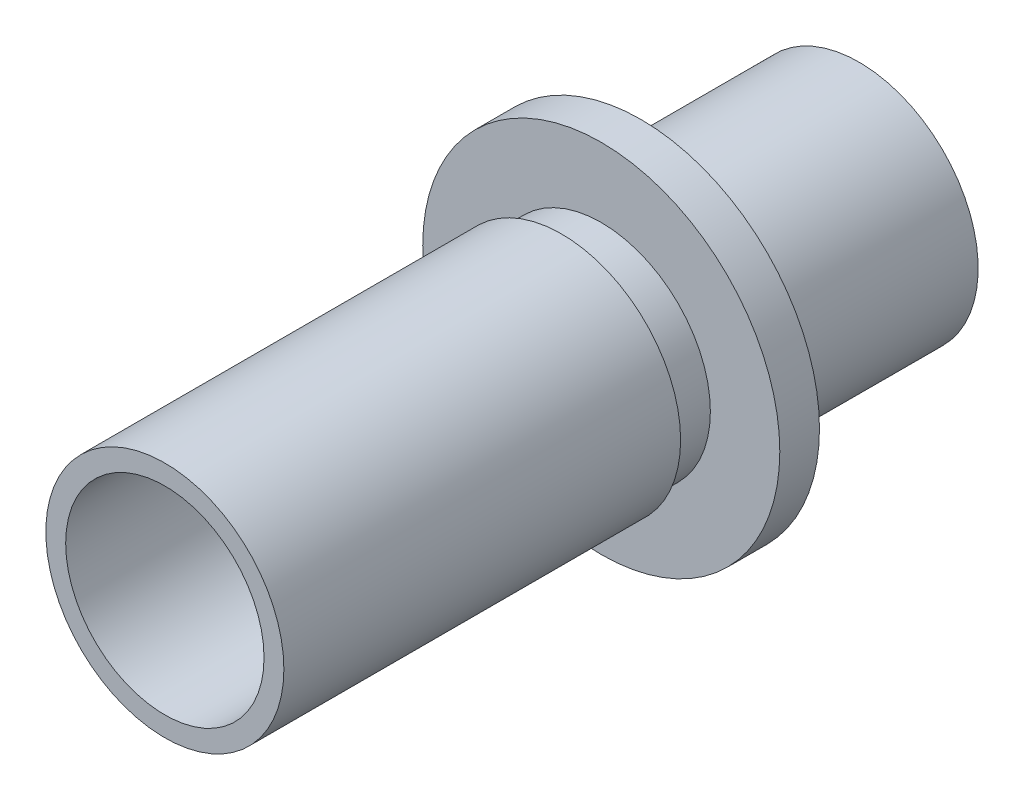
SolidWorks part; units mm, degrees
ref_plane "Plan de face" through (0, 0, 0) normal (0, 0, 1) x (1, 0, 0)
ref_plane "Plan de dessus" through (0, 0, 0) normal (0, 1, 0) x (1, 0, 0)
ref_plane "Plan de droite" through (0, 0, 0) normal (1, 0, 0) x (0, 0, -1)
sketch "Esquisse1" plane through (0, 0, 0) normal (0, 0, 1) x (1, 0, 0)
  circle A0 centre (0, 0) radius 5
  circle A1 centre (0, 0) radius 6
  dimension "D1" = 10
  dimension "D2" = 12
extrude "Boss.-Extru.1" add sketch "Esquisse1" along normal blind 10
sketch "Esquisse2" plane through (0, 0, 0) normal (0, 0, -1) x (-1, 0, 0)
  circle A0 centre (0, 0) radius 4.5
  circle A1 centre (0, 0) radius 6
  dimension "D1" = 12
  dimension "D2" = 9
extrude "Boss.-Extru.2" add sketch "Esquisse2" along normal blind 1
sketch "Esquisse3" plane through (0, 0, 10) normal (0, 0, 1) x (1, 0, 0)
  circle A0 centre (0, 0) radius 5
  circle A1 centre (0, 0) radius 9
  dimension "D1" = 10
  dimension "D2" = 18
extrude "Boss.-Extru.3" add sketch "Esquisse3" along normal blind 2
sketch "Esquisse4" plane through (0, 0, 12) normal (0, 0, 1) x (1, 0, 0)
  circle A0 centre (0, 0) radius 5
  circle A1 centre (0, 0) radius 5.5
  dimension "D1" = 10
  dimension "D2" = 11
extrude "Boss.-Extru.4" add sketch "Esquisse4" along normal blind 2
sketch "Esquisse5" plane through (0, 0, 14) normal (0, 0, 1) x (1, 0, 0)
  circle A0 centre (0, 0) radius 6
  circle A1 centre (0, 0) radius 5
  dimension "D1" = 10
  dimension "D2" = 12
extrude "Boss.-Extru.5" add sketch "Esquisse5" along normal blind 10
sketch "Esquisse6" plane through (0, 0, 24) normal (0, 0, 1) x (1, 0, 0)
  circle A0 centre (0, 0) radius 5
  circle A1 centre (0, 0) radius 6
  dimension "D1" = 10
  dimension "D2" = 12
extrude "Boss.-Extru.6" add sketch "Esquisse6" along normal blind 10
